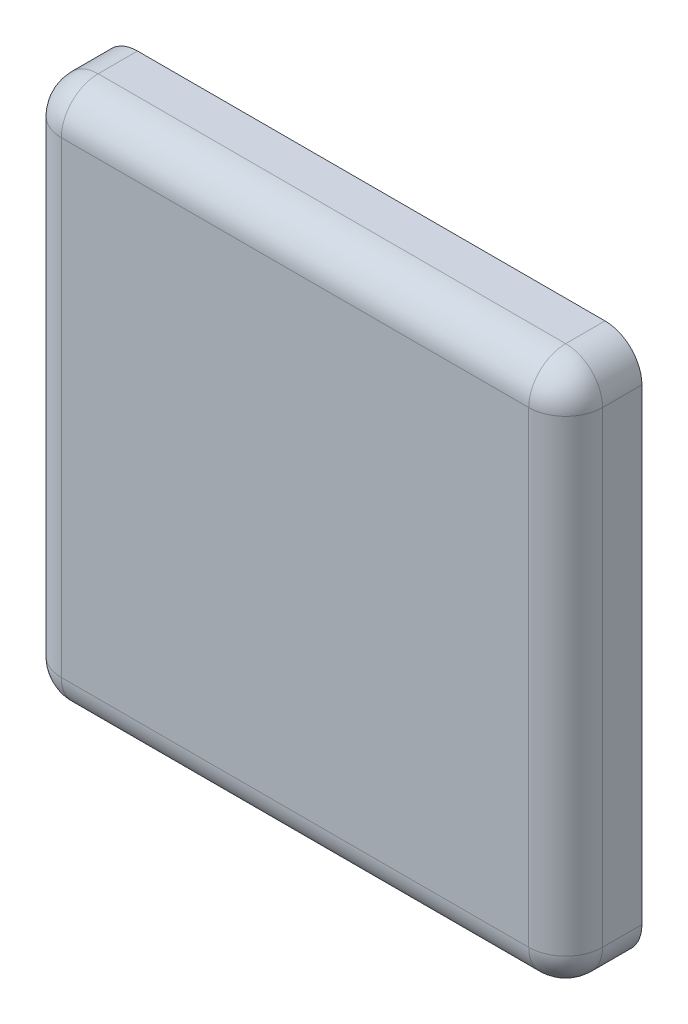
SolidWorks part; units mm, degrees
ref_plane "Front Plane" through (0, 0, 0) normal (0, 0, 1) x (1, 0, 0)
ref_plane "Top Plane" through (0, 0, 0) normal (0, 1, 0) x (1, 0, 0)
ref_plane "Right Plane" through (0, 0, 0) normal (1, 0, 0) x (0, 0, -1)
sketch "Sketch1" plane through (0, 0, 0) normal (0, 0, 1) x (1, 0, 0)
  line L1 (0, 0) -> (22, 0)
  line L2 (0, 0) -> (0, 22)
  line L3 (0, 22) -> (22, 22)
  line L4 (22, 0) -> (22, 22)
  dimension "D1" = 22
  dimension "D2" = 22
extrude "Extrude1" add sketch "Sketch1" along normal blind 3.1
fillet "Fillet1" radius 1.5 8 edges at (22, 11, 3.1) (11, 0, 3.1) (0, 11, 3.1) (11, 22, 3.1) (22, 0, 1.55) (0, 0, 1.55) (0, 22, 1.55) (22, 22, 1.55)
